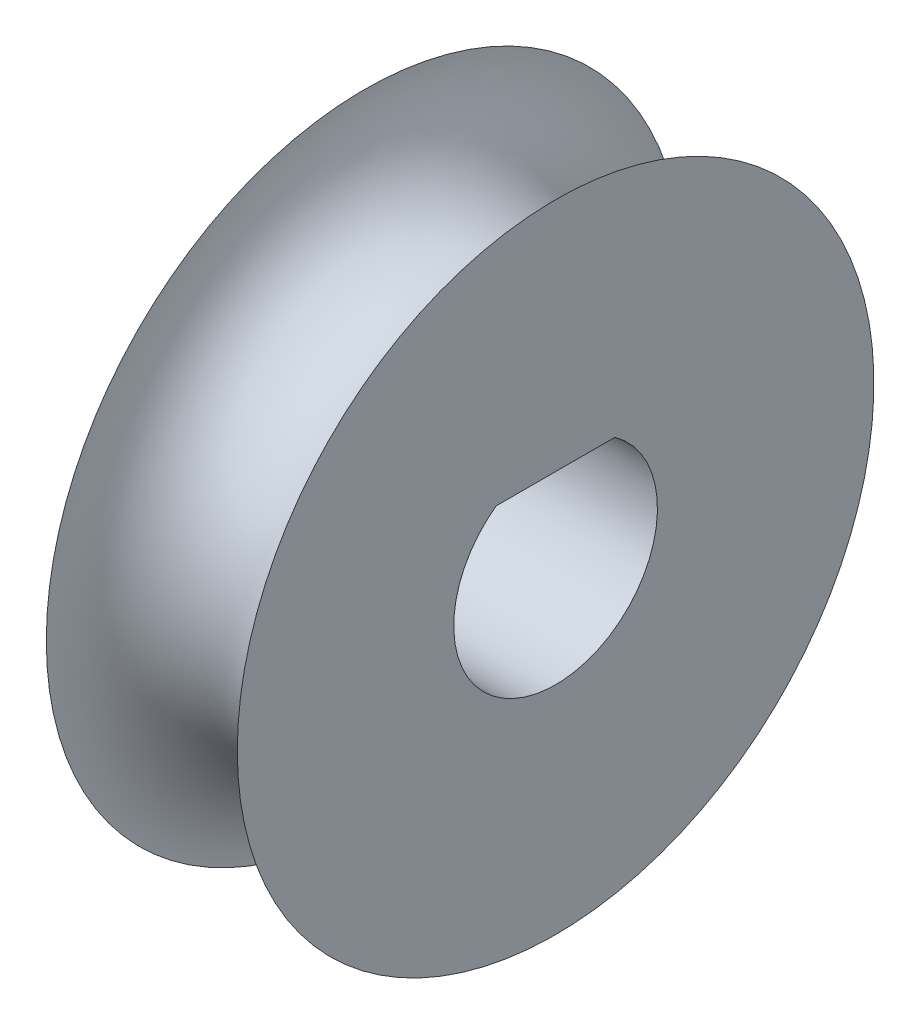
SolidWorks part; units mm, degrees
ref_plane "Front Plane" through (0, 0, 0) normal (0, 0, 1) x (1, 0, 0)
ref_plane "Top Plane" through (0, 0, 0) normal (0, 1, 0) x (1, 0, 0)
ref_plane "Right Plane" through (0, 0, 0) normal (1, 0, 0) x (0, 0, -1)
sketch "Sketch1" plane through (0, 0, 0) normal (0, 0, 1) x (1, 0, 0)
  line L0 (0, 0) -> (0, 8.89) construction
  line L1 (0, 0) -> (0, 8.89) construction
  line L3 (-3.81, 12.7) -> (-3.81, 0)
  line L4 (-3.81, 0) -> (3.81, 0)
  line L5 (3.81, 12.7) -> (3.81, 0)
  arc A0 (-3.81, 12.7) -> (3.81, 12.7) centre (0, 12.7) ccw
  point P3 (0, 9.525)
  dimension "D1" = 12.7
  dimension "D2" = 7.62
revolve "Revolve1" add sketch "Sketch1" angle 360 about L4
sketch "Sketch2" plane through (3.81, 0, 0) normal (1, 0, 0) x (0, 0, -1)
  line L0 (0, 4.064) -> (0, 3.302) construction
  line L1 (-2.3692, 3.302) -> (2.3692, 3.302)
  arc A0 (-2.3692, 3.302) -> (2.3692, 3.302) centre (0, 0) ccw
  point P8 (0, 3.302)
  dimension "D1" = 8.128
extrude "Cut-Extrude1" cut sketch "Sketch2" against normal through all
